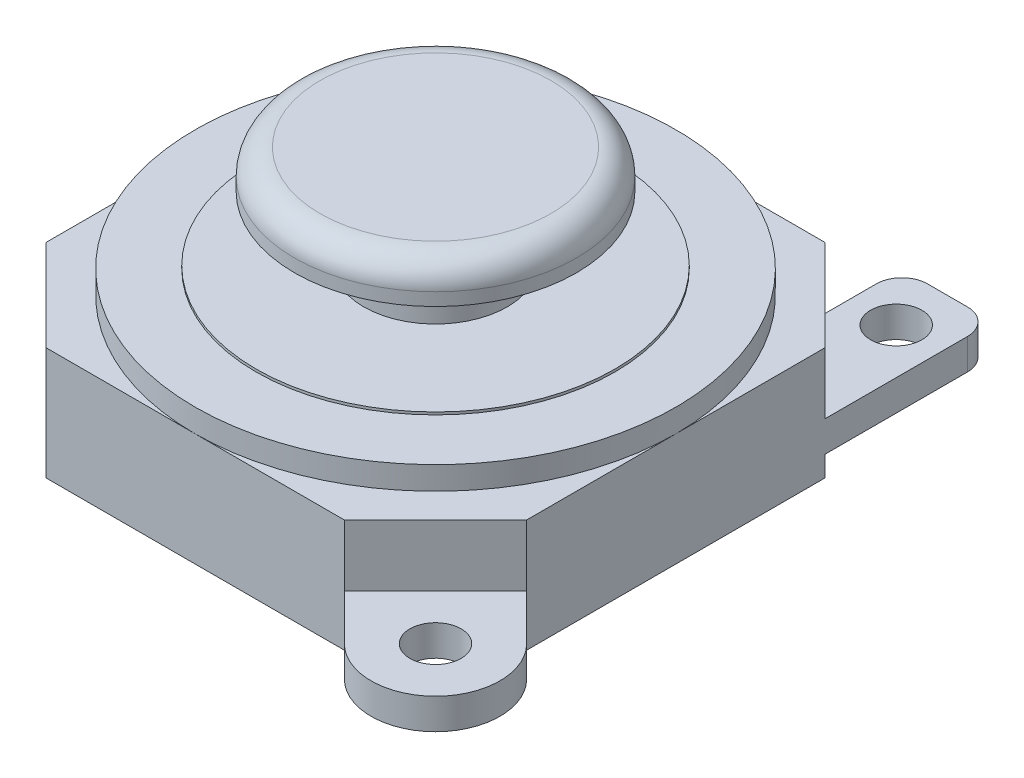
SolidWorks part; units mm, degrees
ref_plane "Front Plane" through (0, 0, 0) normal (0, 0, 1) x (1, 0, 0)
ref_plane "Top Plane" through (0, 0, 0) normal (0, 1, 0) x (1, 0, 0)
ref_plane "Right Plane" through (0, 0, 0) normal (1, 0, 0) x (0, 0, -1)
sketch "Sketch1" plane through (-40.7874, -82.8797, -2.365) normal (0, 1, 0) x (1, 0, 0)
  line L0 (28.0251, 37.9826) -> (31.5811, 34.4266)
  line L1 (16.3871, 37.9826) -> (28.0251, 37.9826)
  line L2 (12.8311, 34.4266) -> (12.8311, 22.7886)
  line L3 (16.3871, 19.2326) -> (28.0251, 19.2326)
  line L4 (31.5811, 34.4266) -> (31.5811, 22.7886)
  line L5 (28.0251, 19.2326) -> (31.5811, 22.7886)
  line L6 (12.8311, 22.7886) -> (16.3871, 19.2326)
  line L7 (12.8311, 34.4266) -> (16.3871, 37.9826)
  point P0 (12.8311, 37.9826)
  point P1 (31.5811, 19.2326)
  point P2 (12.8311, 19.2326)
  point P3 (31.5811, 37.9826)
  dimension "D1" = 18.75
  dimension "D2" = 18.75
  dimension "D3" = 3.556
  dimension "D4" = 3.556
  dimension "D6" = 3.556
  dimension "D7" = 3.556
  dimension "D8" = 3.556
  dimension "D9" = 3.556
extrude "Boss-Extrude1" add sketch "Sketch1" along normal blind 4.4
sketch "Sketch2" plane through (0, -78.4797, 0) normal (0, 1, 0) x (1, 0, 0)
  line L0 (-9.2063, 30.9726) -> (-27.9563, 30.9726) construction
  line L1 (-9.2063, 25.1536) -> (-9.2063, 36.7916) construction
  line L2 (-27.9563, 36.7916) -> (-27.9563, 25.1536) construction
  line L3 (-12.7623, 40.3476) -> (-24.4003, 40.3476) construction
  circle A0 centre (-18.5813, 30.9726) radius 9.375
extrude "Boss-Extrude2" add sketch "Sketch2" along normal blind 0.9
sketch "Sketch3" plane through (0, -77.5797, 0) normal (0, 1, 0) x (1, 0, 0)
  line L0 (-9.2063, 30.9726) -> (-27.9563, 30.9726) construction
  circle A0 centre (-18.5813, 30.9726) radius 9.375 construction
  circle A1 centre (-18.5813, 30.9726) radius 7
extrude "Boss-Extrude3" add sketch "Sketch3" along normal blind 0.1
sketch "Sketch4" plane through (0, -77.4797, 0) normal (0, 1, 0) x (1, 0, 0)
  line L0 (-11.5813, 30.9726) -> (-25.5813, 30.9726) construction
  circle A0 centre (-18.5813, 30.9726) radius 7 construction
  circle A1 centre (-18.5813, 30.9726) radius 2.8
extrude "Boss-Extrude4" add sketch "Sketch4" along normal blind 2.5
sketch "Sketch5" plane through (0, -74.9797, 0) normal (0, 1, 0) x (1, 0, 0)
  circle A0 centre (-18.5813, 30.9726) radius 5.5
extrude "Boss-Extrude5" add sketch "Sketch5" along normal blind 1.5
fillet "Fillet1" radius 1 1 edges at (-18.5813, -73.4797, -25.4726)
sketch "Sketch6" plane through (0, -82.8797, 0) normal (0, -1, 0) x (1, 0, 0)
  line L0 (-12.7623, -21.5976) -> (-10.9843, -19.8196)
  line L2 (-9.2063, -25.1536) -> (-7.4283, -23.3756)
  line L3 (-12.7623, -21.5976) -> (-9.2063, -25.1536) construction
  line L4 (-10.9843, -19.8196) -> (-7.4283, -23.3756) construction
  circle A0 centre (-9.2063, -21.5976) radius 2.5145
  circle A1 centre (-9.2063, -21.5976) radius 1
  line M7 (-9.2063, -25.1536) -> (-12.7623, -21.5976)
extrude "Boss-Extrude6" add sketch "Sketch6" against normal blind 1.2 from offset 0.8 contours A0 L4 A1 | L4 A0 A1 | A0 L0 M7 | A0 L2 M7 offset against normal yes
sketch "Sketch7" plane through (0, -82.0797, 0) normal (0, -1, 0) x (1, 0, 0)
  line L0 (-9.2063, -36.7916) -> (-9.2063, -42.3476)
  line L1 (-9.2063, -25.1536) -> (-9.2063, -36.7916) construction
  line L2 (-10.2063, -43.3476) -> (-11.7623, -43.3476)
  line L3 (-12.7623, -42.3476) -> (-12.7623, -40.3476)
  line L4 (-10.9843, -43.3476) -> (-10.9843, -38.0878) construction
  line L5 (-9.2063, -36.7916) -> (-12.7623, -40.3476)
  arc A0 (-11.7623, -43.3476) -> (-12.7623, -42.3476) centre (-11.7623, -42.3476) cw
  arc A1 (-9.2063, -42.3476) -> (-10.2063, -43.3476) centre (-10.2063, -42.3476) cw
  circle A3 centre (-10.9843, -41.3476) radius 1
  dimension "D1" = 1
  dimension "D2" = 2
  dimension "D3" = 3
extrude "Boss-Extrude7" add sketch "Sketch7" against normal up to surface (1.2 mm away)
